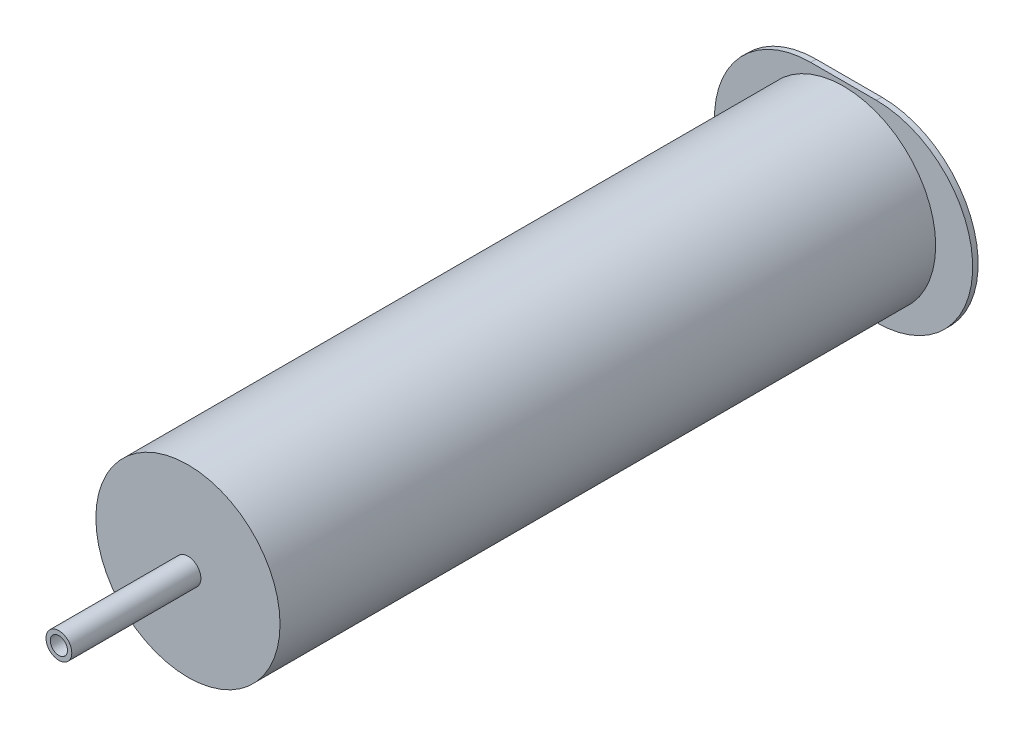
SolidWorks part; units mm, degrees
ref_plane "Front Plane" through (0, 0, 0) normal (0, 0, 1) x (1, 0, 0)
ref_plane "Top Plane" through (0, 0, 0) normal (0, 1, 0) x (1, 0, 0)
ref_plane "Right Plane" through (0, 0, 0) normal (1, 0, 0) x (0, 0, -1)
sketch "Sketch1" plane through (0, 0, 0) normal (0, 0, 1) x (1, 0, 0)
  line L0 (-7.64, 0) -> (7.64, 0) construction
  line L1 (-7.64, 22.37) -> (7.64, 22.37)
  line L2 (-7.64, -22.37) -> (7.64, -22.37)
  arc A1 (-7.64, 22.37) -> (-7.64, -22.37) centre (-7.64, 0) ccw
  arc A2 (7.64, -22.37) -> (7.64, 22.37) centre (7.64, 0) ccw
  point P2 (0, 0)
  point P4 (0, 0)
  point P9 (30.01, 0)
  point P10 (-30.01, 0)
  dimension "D1" = 60.02
  dimension "D2" = 44.74
extrude "Boss-Extrude1" add sketch "Sketch1" along normal blind 1.27
sketch "Sketch2" plane through (0, 0, 1.27) normal (0, 0, 1) x (1, 0, 0)
  circle A0 centre (0, 0) radius 21.405
  dimension "D1" = 42.81
extrude "Boss-Extrude2" add sketch "Sketch2" along normal blind 152.4
sketch "Sketch3" plane through (0, 0, 0) normal (0, 0, -1) x (-1, 0, 0)
  circle A0 centre (0, 0) radius 20.5
  dimension "D1" = 41
extrude "Cut-Extrude1" cut sketch "Sketch3" against normal blind 149.86
sketch "Sketch4" plane through (0, 0, 153.67) normal (0, 0, 1) x (1, 0, 0)
  circle A0 centre (0, 0) radius 3
  circle A1 centre (0, 0) radius 2
  dimension "D1" = 6
  dimension "D2" = 4
extrude "Boss-Extrude3" add sketch "Sketch4" along normal blind 30
